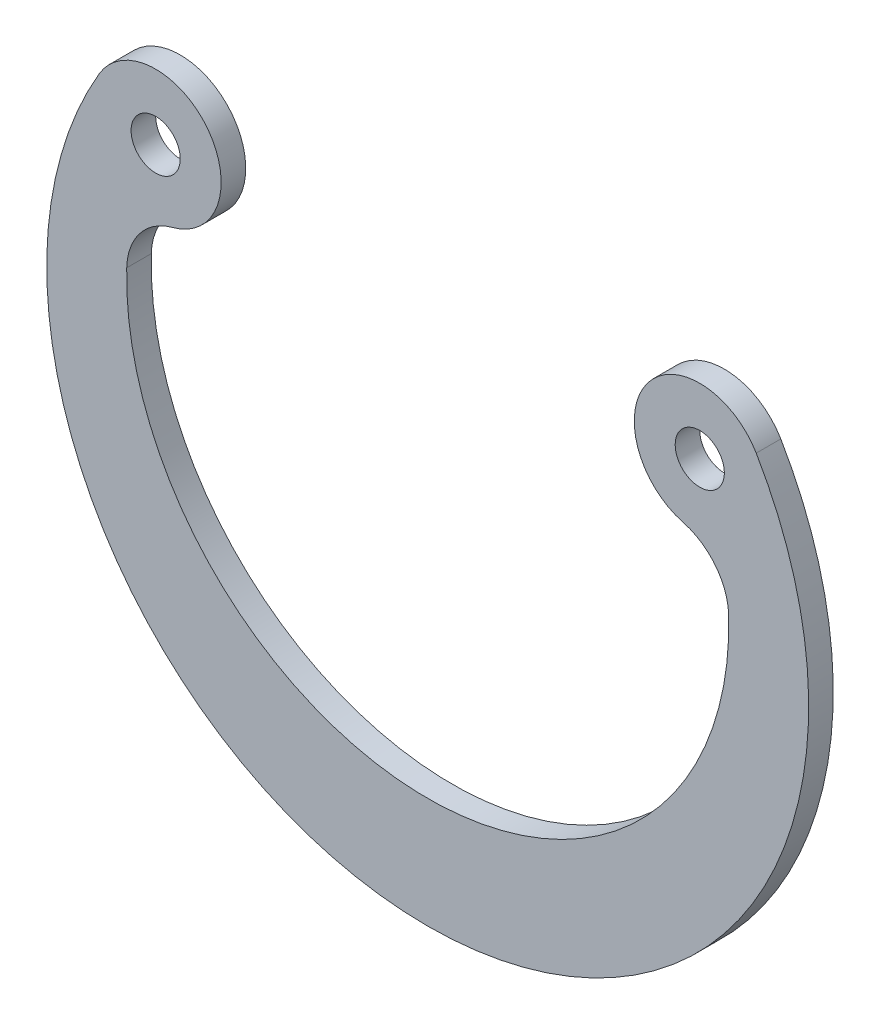
SolidWorks part; units mm, degrees
ref_plane "Спереди" through (0, 0, 0) normal (0, 0, 1) x (1, 0, 0)
ref_plane "Сверху" through (0, 0, 0) normal (0, 1, 0) x (1, 0, 0)
ref_plane "Справа" through (0, 0, 0) normal (1, 0, 0) x (0, 0, -1)
sketch "Эскиз1" plane through (0, 0, 0) normal (0, 0, 1) x (1, 0, 0)
  arc A0 (-13.3656, 7.8493) -> (13.3656, 7.8493) centre (0, 0) ccw
  arc A1 (13.3656, 7.8493) -> (10.3862, 3.9242) centre (11.068, 6.5) ccw
  arc A2 (10.3862, 3.9242) -> (12.2457, 1.5734) centre (9.7466, 1.5074) cw
  arc A3 (12.2457, 1.5734) -> (-12.2457, 1.5734) centre (0, 1.25) cw
  arc A4 (-12.2457, 1.5734) -> (-10.3862, 3.9242) centre (-9.7466, 1.5074) cw
  arc A5 (-10.3862, 3.9242) -> (-13.3656, 7.8493) centre (-11.068, 6.5) ccw
  circle A6 centre (-11.068, 6.5) radius 1
  circle A7 centre (11.068, 6.5) radius 1
extrude "Бобышка-Вытянуть1" add sketch "Эскиз1" against normal blind 1
